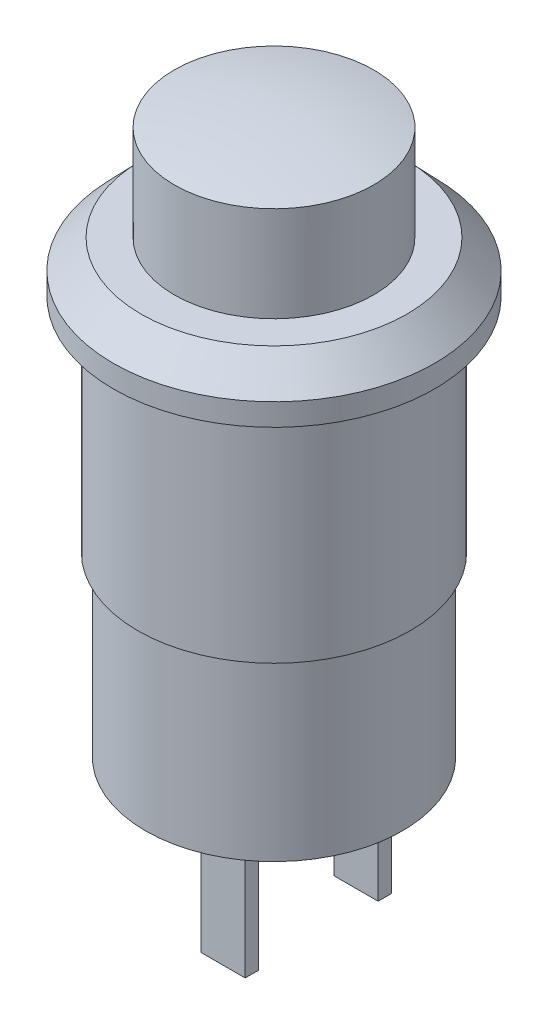
SolidWorks part; units mm, degrees
ref_plane "Спереди" through (0, 0, 0) normal (0, 0, 1) x (1, 0, 0)
ref_plane "Сверху" through (0, 0, 0) normal (0, 1, 0) x (1, 0, 0)
ref_plane "Справа" through (0, 0, 0) normal (1, 0, 0) x (0, 0, -1)
sketch "Sketch1" plane through (0, 0, 0) normal (0, 0, 1) x (1, 0, 0)
  line L0 (0, 17.9633) -> (0, -22.0711) construction
  line L1 (-17.2642, 0) -> (17.5389, 0) construction
  line L3 (-4.5, 6.6) -> (-4.5, 2.3)
  line L4 (-4.5, 2.3) -> (-6, 2.3)
  line L5 (-6, 2.3) -> (-7.25, 1)
  line L6 (-7.25, 1) -> (-7.25, 0)
  line L7 (-7.25, 0) -> (-6.15, 0)
  line L8 (-6.15, 0) -> (-6.15, -10)
  line L9 (-6.15, -10) -> (-5.8, -10)
  line L10 (-5.8, -10) -> (-5.8, -18)
  line L11 (-5.8, -18) -> (0, -18)
  line L12 (0, -18) -> (0, 7.1)
  arc A0 (-4.5, 6.6) -> (0, 7.1) centre (0, -13.4) cw
  dimension "D11" = 0.5
  dimension "D1" = 9
  dimension "D2" = 14.5
  dimension "D3" = 12.3
  dimension "D4" = 11.6
  dimension "D5" = 4.3
  dimension "D6" = 2.3
  dimension "D7" = 1
  dimension "D8" = 1.5
  dimension "D9" = 18
  dimension "D10" = 10
revolve "Revolve1" add sketch "Sketch1" angle 360 about L0
sketch "Sketch2" plane through (0, -18, 0) normal (0, -1, 0) x (1, 0, 0)
  line L0 (0, 5.8) -> (0, -5.8) construction
  line L1 (-5.8, 0) -> (5.8, 0) construction
  line L2 (0, 3.3) -> (2, 3.3)
  line L3 (0, 3.3) -> (0, 2.7)
  line L4 (0, 2.7) -> (2, 2.7)
  line L5 (2, 3.3) -> (2, 2.7)
  line L6 (0, -2.7) -> (2, -2.7)
  line L7 (0, -2.7) -> (0, -3.3)
  line L8 (0, -3.3) -> (2, -3.3)
  line L9 (2, -2.7) -> (2, -3.3)
  circle A0 centre (0, 0) radius 5.8 construction
  circle A1 centre (0, 0) radius 5.8 construction
  dimension "D1" = 5.4
  dimension "D2" = 0.6
  dimension "D3" = 2
extrude "Boss-Extrude1" add sketch "Sketch2" along normal blind 6
